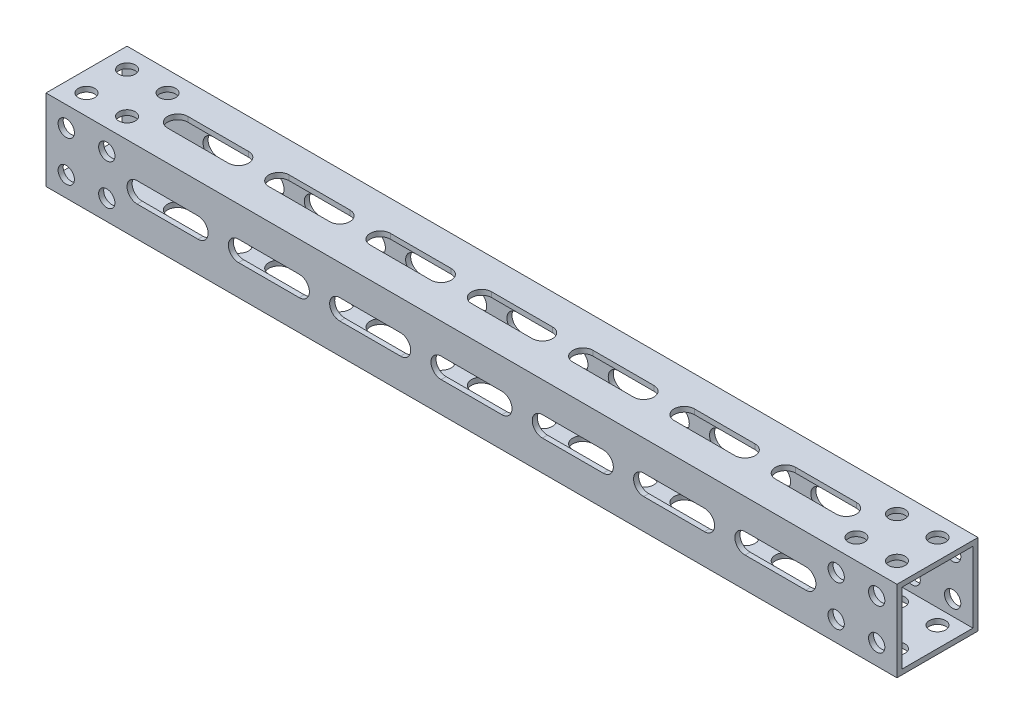
SolidWorks part; units mm, degrees
material "6061-T6 (SS)"
ref_plane "Front" through (0, 0, 0) normal (0, 0, 1) x (1, 0, 0)
ref_plane "Top" through (0, 0, 0) normal (0, 1, 0) x (1, 0, 0)
ref_plane "Right" through (0, 0, 0) normal (1, 0, 0) x (0, 0, -1)
sketch "Sketch1" plane through (0, 0, 0) normal (1, 0, 0) x (0, 0, -1)
  line L1 (12.7, -12.7) -> (-12.7, -12.7)
  line L2 (12.7, -12.7) -> (12.7, 12.7)
  line L3 (12.7, 12.7) -> (-12.7, 12.7)
  line L4 (-12.7, -12.7) -> (-12.7, 12.7)
  line L5 (12.7, -12.7) -> (-12.7, 12.7) construction
  line L6 (12.7, 12.7) -> (-12.7, -12.7) construction
  point P0 (0, 0)
  dimension "D1" = 25.4
extrude "Extrude-Thin1" add sketch "Sketch1" along normal up to surface (266.7 mm away) thin
sketch "Sketch2" plane through (0, 12.7, 0) normal (0, 1, 0) x (1, 0, 0)
  line L0 (47.625, 0) -> (28.575, 0) construction
  line L1 (47.625, -3.175) -> (28.575, -3.175)
  line L2 (47.625, 3.175) -> (28.575, 3.175)
  line L3 (79.375, 0) -> (60.325, 0) construction
  line L4 (79.375, -3.175) -> (60.325, -3.175)
  line L5 (79.375, 3.175) -> (60.325, 3.175)
  line L6 (111.125, 0) -> (92.075, 0) construction
  line L7 (111.125, -3.175) -> (92.075, -3.175)
  line L8 (111.125, 3.175) -> (92.075, 3.175)
  line L9 (142.875, 0) -> (123.825, 0) construction
  line L10 (142.875, -3.175) -> (123.825, -3.175)
  line L11 (142.875, 3.175) -> (123.825, 3.175)
  line L12 (174.625, 0) -> (155.575, 0) construction
  line L13 (174.625, -3.175) -> (155.575, -3.175)
  line L14 (174.625, 3.175) -> (155.575, 3.175)
  line L15 (206.375, 0) -> (187.325, 0) construction
  line L16 (206.375, -3.175) -> (187.325, -3.175)
  line L17 (206.375, 3.175) -> (187.325, 3.175)
  line L18 (0, 12.7) -> (0, -12.7) construction
  line L19 (238.125, 0) -> (219.075, 0) construction
  line L20 (238.125, -3.175) -> (219.075, -3.175)
  line L21 (238.125, 3.175) -> (219.075, 3.175)
  line L22 (266.7, -12.7) -> (266.7, 12.7) construction
  arc A0 (47.625, -3.175) -> (47.625, 3.175) centre (47.625, 0) ccw
  arc A1 (28.575, 3.175) -> (28.575, -3.175) centre (28.575, 0) ccw
  arc A2 (79.375, -3.175) -> (79.375, 3.175) centre (79.375, 0) ccw
  arc A3 (60.325, 3.175) -> (60.325, -3.175) centre (60.325, 0) ccw
  arc A4 (111.125, -3.175) -> (111.125, 3.175) centre (111.125, 0) ccw
  arc A5 (92.075, 3.175) -> (92.075, -3.175) centre (92.075, 0) ccw
  arc A6 (142.875, -3.175) -> (142.875, 3.175) centre (142.875, 0) ccw
  arc A7 (123.825, 3.175) -> (123.825, -3.175) centre (123.825, 0) ccw
  arc A8 (174.625, -3.175) -> (174.625, 3.175) centre (174.625, 0) ccw
  arc A9 (155.575, 3.175) -> (155.575, -3.175) centre (155.575, 0) ccw
  arc A10 (206.375, -3.175) -> (206.375, 3.175) centre (206.375, 0) ccw
  arc A11 (187.325, 3.175) -> (187.325, -3.175) centre (187.325, 0) ccw
  arc A12 (238.125, -3.175) -> (238.125, 3.175) centre (238.125, 0) ccw
  arc A13 (219.075, 3.175) -> (219.075, -3.175) centre (219.075, 0) ccw
  point P3 (38.1, 0)
  point P10 (69.85, 0)
  point P18 (101.6, 0)
  point P25 (133.35, 0)
  point P32 (165.1, 0)
  point P39 (196.85, 0)
  point P48 (228.6, 0)
  dimension "D1" = 6.35
  dimension "D2" = 19.05
  dimension "D4" = 28.575
  dimension "D5" = 31.75
  dimension "D6" = 28.575
  dimension "D3" = 7
extrude "Cut-Extrude1" cut sketch "Sketch2" against normal through all
sketch "Sketch3" plane through (0, 0, -12.7) normal (0, 0, -1) x (-1, 0, 0)
  line L0 (-28.575, 0) -> (-47.625, 0) construction
  line L1 (-28.575, -3.175) -> (-47.625, -3.175)
  line L2 (-28.575, 3.175) -> (-47.625, 3.175)
  line L3 (0, -12.7) -> (0, 12.7) construction
  line L4 (-60.325, 0) -> (-79.375, 0) construction
  line L5 (-60.325, -3.175) -> (-79.375, -3.175)
  line L6 (-60.325, 3.175) -> (-79.375, 3.175)
  line L7 (-92.075, 0) -> (-111.125, 0) construction
  line L8 (-92.075, -3.175) -> (-111.125, -3.175)
  line L9 (-92.075, 3.175) -> (-111.125, 3.175)
  line L10 (-123.825, 0) -> (-142.875, 0) construction
  line L11 (-123.825, -3.175) -> (-142.875, -3.175)
  line L12 (-123.825, 3.175) -> (-142.875, 3.175)
  line L13 (-155.575, 0) -> (-174.625, 0) construction
  line L14 (-155.575, -3.175) -> (-174.625, -3.175)
  line L15 (-155.575, 3.175) -> (-174.625, 3.175)
  line L16 (-187.325, 0) -> (-206.375, 0) construction
  line L17 (-187.325, -3.175) -> (-206.375, -3.175)
  line L18 (-187.325, 3.175) -> (-206.375, 3.175)
  line L19 (-219.075, 0) -> (-238.125, 0) construction
  line L20 (-219.075, -3.175) -> (-238.125, -3.175)
  line L21 (-219.075, 3.175) -> (-238.125, 3.175)
  line L22 (-28.575, 0) -> (-60.325, 0) construction
  arc A0 (-28.575, -3.175) -> (-28.575, 3.175) centre (-28.575, 0) ccw
  arc A1 (-47.625, 3.175) -> (-47.625, -3.175) centre (-47.625, 0) ccw
  arc A2 (-60.325, -3.175) -> (-60.325, 3.175) centre (-60.325, 0) ccw
  arc A3 (-79.375, 3.175) -> (-79.375, -3.175) centre (-79.375, 0) ccw
  arc A4 (-92.075, -3.175) -> (-92.075, 3.175) centre (-92.075, 0) ccw
  arc A5 (-111.125, 3.175) -> (-111.125, -3.175) centre (-111.125, 0) ccw
  arc A6 (-123.825, -3.175) -> (-123.825, 3.175) centre (-123.825, 0) ccw
  arc A7 (-142.875, 3.175) -> (-142.875, -3.175) centre (-142.875, 0) ccw
  arc A8 (-155.575, -3.175) -> (-155.575, 3.175) centre (-155.575, 0) ccw
  arc A9 (-174.625, 3.175) -> (-174.625, -3.175) centre (-174.625, 0) ccw
  arc A10 (-187.325, -3.175) -> (-187.325, 3.175) centre (-187.325, 0) ccw
  arc A11 (-206.375, 3.175) -> (-206.375, -3.175) centre (-206.375, 0) ccw
  arc A12 (-219.075, -3.175) -> (-219.075, 3.175) centre (-219.075, 0) ccw
  arc A13 (-238.125, 3.175) -> (-238.125, -3.175) centre (-238.125, 0) ccw
  point P3 (-38.1, 0)
  point P13 (-69.85, 0)
  point P20 (-101.6, 0)
  point P27 (-133.35, 0)
  point P34 (-165.1, 0)
  point P41 (-196.85, 0)
  point P48 (-228.6, 0)
  dimension "D2" = 19.05
  dimension "D3" = 28.575
  dimension "D1" = 6.35
  dimension "D5" = 31.75
  dimension "D4" = 7
extrude "Cut-Extrude2" cut sketch "Sketch3" against normal through all
sketch "Sketch6" plane through (0, 0, 12.7) normal (0, 0, 1) x (1, 0, 0)
  line L0 (0, 0) -> (12.1609, 0) construction
  line L1 (0, 12.7) -> (0, -12.7) construction
  line L3 (266.7, 12.7) -> (0, 12.7) construction
  line L4 (133.35, -12.7) -> (133.35, 36.0977) construction
  line L5 (266.7, -12.7) -> (0, -12.7) construction
  point P0 (6.35, 6.35)
  point P2 (19.05, 6.35)
  point P11 (19.05, -6.35)
  point P12 (6.35, -6.35)
  point P21 (260.35, -6.35)
  point P22 (247.65, -6.35)
  point P23 (247.65, 6.35)
  point P24 (260.35, 6.35)
  dimension "D1" = 6.35
  dimension "D2" = 6.35
  dimension "D3" = 12.7
hole_wizard "#10 Clearance Hole1" positions "Sketch6" profile "Sketch5" hole size "#10" standard "ANSI Inch" end condition through all
sketch "Sketch5" plane through (6.35, 6.35, 12.7) normal (1, 0, 0) x (0, -1, 0)
  line L0 (0, 0) -> (0, 25.4)
  line L1 (0, 25.4) -> (2.5527, 25.4)
  line L2 (2.5527, 25.4) -> (2.5527, 0)
  line L5 (2.5527, 0) -> (0, 0)
  line L11 (0, -6.35) -> (0, 107.95) construction
  dimension "Thru Hole Dia." = 5.1054
  dimension "Thru Hole Depth" = 25.4
sketch "Sketch9" plane through (0, 12.7, 0) normal (0, 1, 0) x (1, 0, 0)
  line L0 (0, 0) -> (13.3717, 0) construction
  line L1 (0, 12.7) -> (0, -12.7) construction
  line L4 (133.35, -12.7) -> (133.35, 19.8462) construction
  line L5 (266.7, -12.7) -> (0, -12.7) construction
  line L7 (266.7, 12.7) -> (0, 12.7) construction
  point P0 (6.35, 6.35)
  point P2 (19.05, 6.35)
  point P20 (19.05, -6.35)
  point P21 (6.35, -6.35)
  point P22 (260.35, -6.35)
  point P23 (247.65, -6.35)
  point P24 (247.65, 6.35)
  point P25 (260.35, 6.35)
  dimension "D1" = 6.35
  dimension "D2" = 6.35
  dimension "D3" = 12.7
hole_wizard "#10 Clearance Hole2" positions "Sketch9" profile "Sketch8" hole size "#10" standard "ANSI Inch" end condition through all
sketch "Sketch8" plane through (6.35, 12.7, -6.35) normal (1, 0, 0) x (0, 0, 1)
  line L0 (0, 0) -> (0, 25.4)
  line L1 (0, 25.4) -> (2.5527, 25.4)
  line L2 (2.5527, 25.4) -> (2.5527, 0)
  line L5 (2.5527, 0) -> (0, 0)
  line L11 (0, -6.35) -> (0, 107.95) construction
  dimension "Thru Hole Dia." = 5.1054
  dimension "Thru Hole Depth" = 25.4
